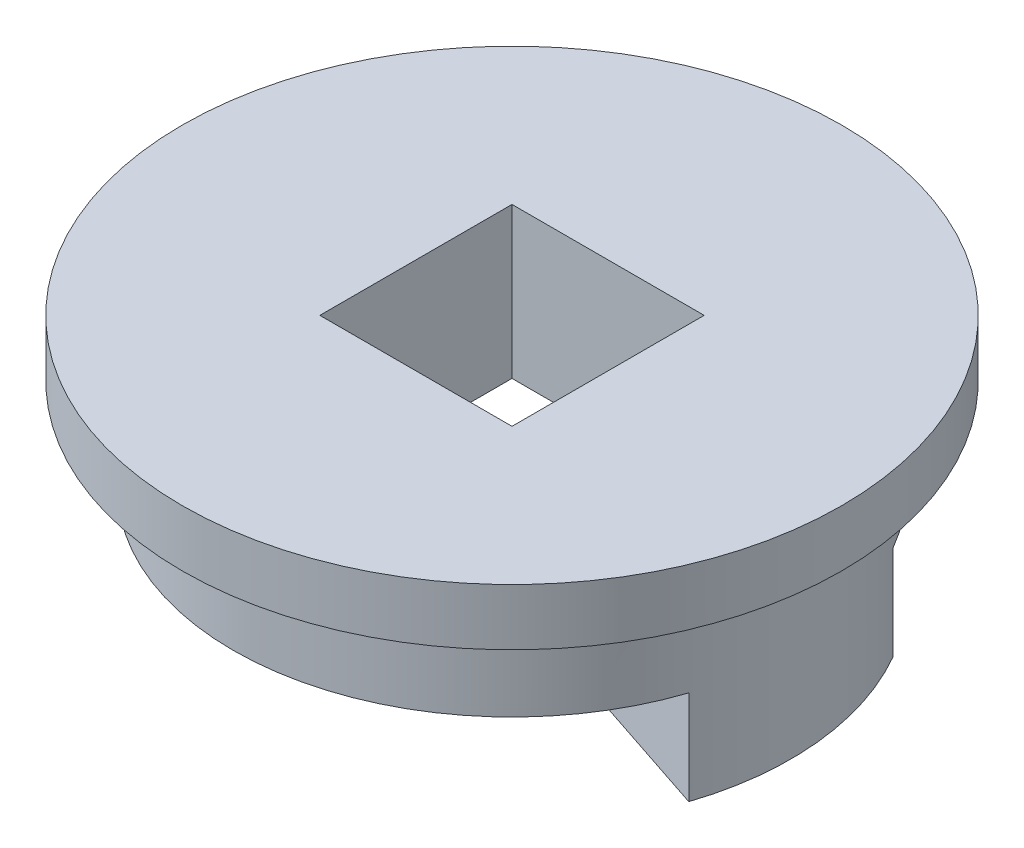
SolidWorks part; units mm, degrees
ref_plane "Спереди" through (0, 0, 0) normal (0, 0, 1) x (1, 0, 0)
ref_plane "Сверху" through (0, 0, 0) normal (0, 1, 0) x (1, 0, 0)
ref_plane "Справа" through (0, 0, 0) normal (1, 0, 0) x (0, 0, -1)
sketch "Эскиз1" plane through (0, 0, 0) normal (0, 1, 0) x (1, 0, 0)
  circle A0 centre (0, 0) radius 14.8
  dimension "D1" = 29.6
extrude "Бобышка-Вытянуть1" add sketch "Эскиз1" along normal blind 5
sketch "Эскиз2" plane through (0, 5, 0) normal (0, 1, 0) x (1, 0, 0)
  circle A0 centre (0, 0) radius 17.5
  dimension "D1" = 35
extrude "Бобышка-Вытянуть2" add sketch "Эскиз2" along normal blind 3
sketch "Эскиз3" plane through (0, 8, 0) normal (0, 1, 0) x (1, 0, 0)
  line L1 (-5.1, -5.1) -> (5.1, -5.1)
  line L2 (-5.1, -5.1) -> (-5.1, 5.1)
  line L3 (-5.1, 5.1) -> (5.1, 5.1)
  line L4 (5.1, -5.1) -> (5.1, 5.1)
  line L5 (-5.1, -5.1) -> (5.1, 5.1) construction
  line L6 (-5.1, 5.1) -> (5.1, -5.1) construction
  point P0 (0, 0)
  dimension "D1" = 10.2
  dimension "D2" = 10.2
extrude "Вырез-Вытянуть1" cut sketch "Эскиз3" against normal through all
sketch "Эскиз4" plane through (0, 0, 0) normal (0, -1, 0) x (1, 0, 0)
  line L0 (0, 0) -> (15.1554, 8.75) construction
  line L1 (0, 0) -> (15.1554, -8.75) construction
  line L2 (15.1554, 8.75) -> (15.1554, -8.75) construction
  line L3 (0, 0) -> (14.0461, 4.6633) construction
  line L4 (5.1, 5.1) -> (5.1, -5.1) construction
  line L5 (14.0461, 4.6633) -> (5.1, 1.6932)
  line L6 (5.1, -2.9445) -> (12.8172, -7.4)
  line L7 (5.1, 1.6932) -> (5.1, -2.9445)
  circle A0 centre (0, 0) radius 17.5 construction
  circle A2 centre (0, 0) radius 14.8 construction
  circle A3 centre (0, 0) radius 14.8 construction
  arc A4 (14.0461, 4.6633) -> (12.8172, -7.4) centre (0, 0) cw
  point P5 (12.8172, 7.4)
  point P7 (5.1, 1.6932)
  point P8 (12.8172, -7.4)
  point P11 (5.1, -2.9445)
  dimension "D1" = 60
  dimension "D2" = 3
extrude "Бобышка-Вытянуть3" add sketch "Эскиз4" along normal blind 5
